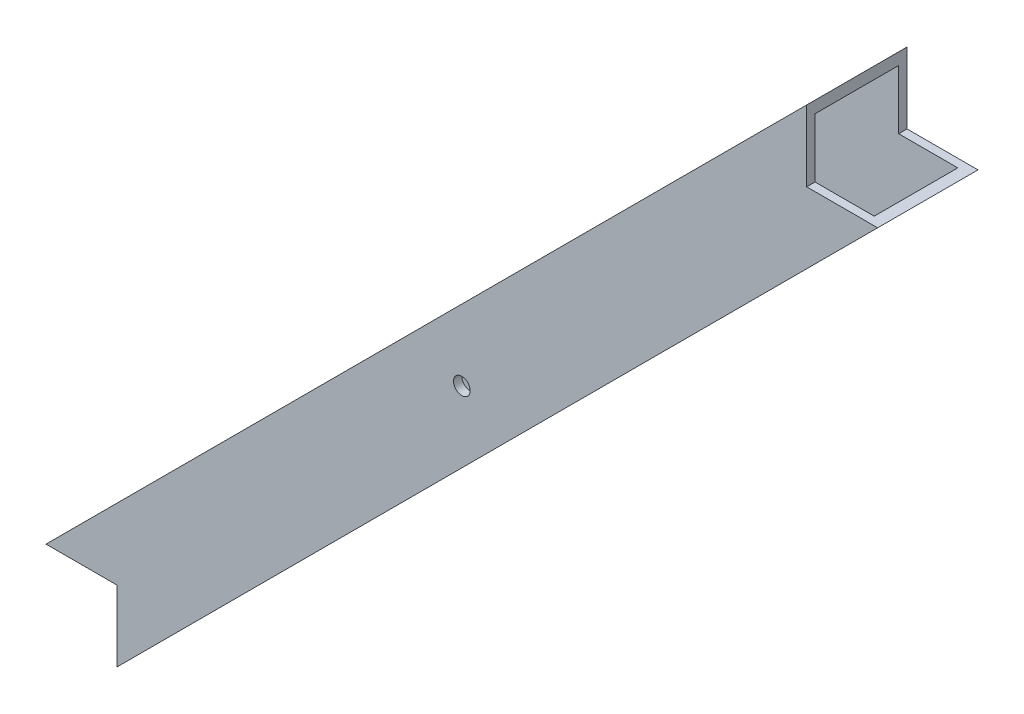
SolidWorks part; units mm, degrees
ref_plane "Front Plane" through (0, 0, 0) normal (0, 0, 1) x (1, 0, 0)
ref_plane "Top Plane" through (0, 0, 0) normal (0, 1, 0) x (1, 0, 0)
ref_plane "Right Plane" through (0, 0, 0) normal (1, 0, 0) x (0, 0, -1)
sketch "Sketch1" plane through (0, 0, 0) normal (0, 0, 1) x (1, 0, 0)
  line L0 (300, 300) -> (0, 0) construction
  line L1 (0, 0) -> (19.05, 0) construction
  line L2 (0, 0) -> (0, 19.05) construction
  line L3 (0, 300) -> (273.0592, 300) construction
  line L4 (300, 0) -> (300, 273.0592) construction
  line L5 (-19.05, -19.05) -> (19.05, -19.05) construction
  line L6 (-19.05, -19.05) -> (-19.05, 19.05) construction
  line L7 (-19.05, 19.05) -> (19.05, 19.05) construction
  line L8 (19.05, -19.05) -> (19.05, 19.05) construction
  line L9 (-19.05, -19.05) -> (19.05, 19.05) construction
  line L10 (-19.05, 19.05) -> (19.05, -19.05) construction
  line L11 (319.05, 319.05) -> (280.95, 319.05) construction
  line L12 (319.05, 319.05) -> (319.05, 280.95) construction
  line L13 (319.05, 280.95) -> (280.95, 280.95) construction
  line L14 (280.95, 319.05) -> (280.95, 280.95) construction
  line L15 (319.05, 319.05) -> (280.95, 280.95) construction
  line L16 (319.05, 280.95) -> (280.95, 319.05) construction
  line L17 (136.5296, 163.4704) -> (163.4704, 136.5296) construction
  line L18 (150.5853, 177.5261) -> (136.5296, 163.4704) construction
  line L19 (163.4704, 136.5296) -> (205.9698, 179.0291) construction
  line L20 (19.05, -7.8908) -> (307.8908, 280.95)
  line L21 (280.95, 307.8908) -> (-7.8908, 19.05)
  line L22 (280.95, 307.8908) -> (280.95, 280.95)
  line L23 (280.95, 280.95) -> (307.8908, 280.95)
  line L24 (19.05, -7.8908) -> (19.05, 19.05)
  line L25 (19.05, 19.05) -> (-7.8908, 19.05)
  line L26 (0, 26.9408) -> (0, 300) construction
  line L27 (26.9408, 0) -> (300, 0) construction
  line L28 (300, 280.95) -> (300, 300) construction
  line L29 (280.95, 300) -> (300, 300) construction
  circle A0 centre (150, 150) radius 3.175
  point P15 (150, 150)
  point P16 (307.8908, 280.95)
  point P18 (150, 150)
  point P20 (280.95, 307.8908)
  point P23 (-7.8908, 19.05)
  point P24 (19.05, -7.8908)
  point P25 (19.05, -7.8908)
  point P26 (19.05, -7.8908)
  dimension "D8" = 6.35
  dimension "D1" = 300
  dimension "D2" = 300
  dimension "D3" = 38.1
  dimension "D4" = 38.1
  dimension "D5" = 38.1
  dimension "D6" = 38.1
  dimension "D7" = 38.1
  dimension "D9" = 408.4825
extrude "Boss-Extrude1" add sketch "Sketch1" against normal blind 38.1 contours L25 L24 L1 L20 L23 L22 L21
sketch "Sketch2" plane through (0, 0, -38.1) normal (0, 0, -1) x (-1, 0, 0)
  line L0 (-150, 150) -> (-136.5296, 163.4704)
  line L1 (-280.95, 307.8908) -> (7.8908, 19.05) construction
  point P0 (-150, 150)
ref_plane "Plane1" through (150, 150, 0) normal (-0.7071, -0.7071, 0) x (-0.7071, 0.7071, 0)
sketch "Sketch3" plane through (150, 150, 0) normal (-0.7071, -0.7071, 0) x (-0.7071, 0.7071, 0)
  line L1 (19.05, 38.1) -> (-19.05, 38.1)
  line L2 (19.05, 38.1) -> (19.05, 0)
  line L3 (19.05, 0) -> (-19.05, 0)
  line L4 (-19.05, 38.1) -> (-19.05, 0)
  line L5 (15.875, 3.175) -> (-15.875, 3.175)
  line L6 (15.875, 3.175) -> (15.875, 34.925)
  line L7 (15.875, 34.925) -> (-15.875, 34.925)
  line L8 (-15.875, 3.175) -> (-15.875, 34.925)
  line L9 (15.875, 3.175) -> (-15.875, 34.925) construction
  line L10 (15.875, 34.925) -> (-15.875, 3.175) construction
  point P6 (-19.05, 19.05)
  point P7 (0, 38.1)
  point P8 (0, 19.05)
  point P12 (0, 19.05)
  dimension "D1" = 3.175
extrude "Cut-Extrude1" cut sketch "Sketch3" against normal through all both and the other way through all contours L6 L5 L8 L7
